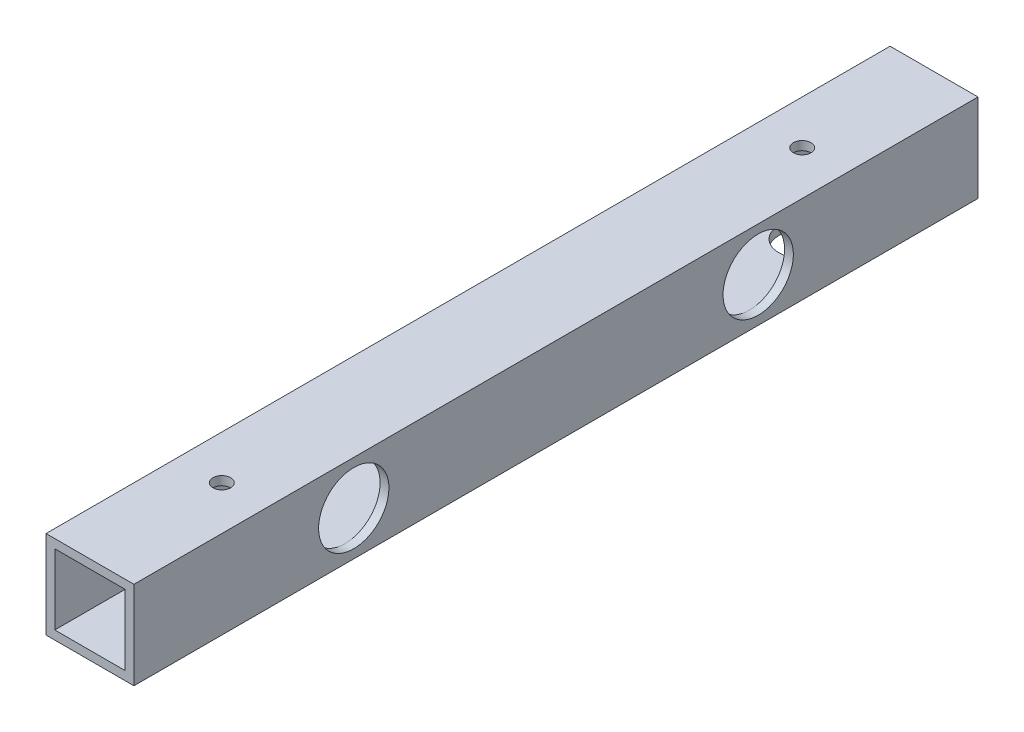
SolidWorks part; units mm, degrees
material "1060 合金"
ref_plane "正面" through (0, 0, 0) normal (0, 0, 1) x (1, 0, 0)
ref_plane "平面" through (0, 0, 0) normal (0, 1, 0) x (1, 0, 0)
ref_plane "右側面" through (0, 0, 0) normal (1, 0, 0) x (0, 0, -1)
sketch "ｽｹｯﾁ1" plane through (0, 0, 0) normal (0, 0, 1) x (1, 0, 0)
  line L1 (-7.0101, 7.7326) -> (7.9899, 7.7326)
  line L2 (-7.0101, 7.7326) -> (-7.0101, -7.2674)
  line L3 (-7.0101, -7.2674) -> (7.9899, -7.2674)
  line L4 (7.9899, 7.7326) -> (7.9899, -7.2674)
  line L9 (-5.5101, 6.2326) -> (6.4899, 6.2326)
  line L10 (-5.5101, 6.2326) -> (-5.5101, -5.7674)
  line L11 (-5.5101, -5.7674) -> (6.4899, -5.7674)
  line L12 (6.4899, 6.2326) -> (6.4899, -5.7674)
  dimension "D1" = 15
  dimension "D2" = 15
  dimension "D3" = 1.5
  dimension "D4" = 1.5
  dimension "D5" = 12
  dimension "D6" = 12
extrude "ﾎﾞｽ - 押し出し2" add sketch "ｽｹｯﾁ1" along normal blind 144
sketch "ｽｹｯﾁ2" plane through (-7.0101, 0, 0) normal (-1, 0, 0) x (0, 0, 1)
  line L0 (0, 0.2326) -> (72.5, 0.2326)
  line L1 (0, 7.7326) -> (0, -7.2674) construction
  circle A0 centre (72.5, 0.2326) radius 1.5
  dimension "D1" = 72.5
extrude "ｶｯﾄ - 押し出し1" cut sketch "ｽｹｯﾁ2" against normal blind 10
sketch "ｽｹｯﾁ3" plane through (0, 7.7326, 0) normal (0, 1, 0) x (1, 0, 0)
  line L0 (0.4899, 0) -> (0.4899, -22.5)
  line L1 (-7.0101, -144) -> (-7.0101, 0) construction
  circle A0 centre (0.4899, -22.5) radius 1.5
  dimension "D2" = 7.5
  dimension "D1" = 22.5
extrude "ｶｯﾄ - 押し出し2" cut sketch "ｽｹｯﾁ3" against normal blind 10
sketch "ｽｹｯﾁ4" plane through (0, 7.7326, 0) normal (0, 1, 0) x (1, 0, 0)
  line L0 (0.4899, -144) -> (0.4899, -121.5)
  line L2 (-7.0101, -144) -> (-7.0101, 0) construction
  circle A0 centre (0.4899, -121.5) radius 1.5
  dimension "D2" = 7.5
  dimension "D1" = 22.5
extrude "ｶｯﾄ - 押し出し4" cut sketch "ｽｹｯﾁ4" against normal blind 10
sketch "ｽｹｯﾁ6" plane through (-7.0101, 0, 0) normal (-1, 0, 0) x (0, 0, 1)
  line L0 (0, 0.2326) -> (7.5, 0.2326)
  line L1 (0, 7.7326) -> (0, -7.2674) construction
  circle A0 centre (7.5, 0.2326) radius 1.5
  dimension "D1" = 7.5
extrude "ｶｯﾄ - 押し出し5" cut sketch "ｽｹｯﾁ6" against normal blind 10
sketch "ｽｹｯﾁ7" plane through (0, -7.2674, 0) normal (0, -1, 0) x (1, 0, 0)
  line L0 (0.4899, 0) -> (0.4899, 22.5)
  line L1 (-7.0101, 0) -> (7.9899, 0) construction
  circle A0 centre (0.4899, 22.5) radius 4
  dimension "D1" = 22.5
extrude "ｶｯﾄ - 押し出し6" cut sketch "ｽｹｯﾁ7" against normal blind 10
sketch "ｽｹｯﾁ8" plane through (0, -7.2674, 0) normal (0, -1, 0) x (1, 0, 0)
  line L0 (0.4899, 144) -> (0.4899, 121.5)
  line L1 (-7.0101, 144) -> (7.9899, 144) construction
  circle A0 centre (0.4899, 121.5) radius 4
  dimension "D1" = 22.5
extrude "ｶｯﾄ - 押し出し7" cut sketch "ｽｹｯﾁ8" against normal blind 10
sketch "ｽｹｯﾁ9" plane through (-7.0101, 0, 0) normal (-1, 0, 0) x (0, 0, 1)
  line L0 (0, 0.2326) -> (37.5, 0.2326)
  line L1 (0, 7.7326) -> (0, -7.2674) construction
  circle A0 centre (37.5, 0.2326) radius 1.5
  dimension "D1" = 37.5
extrude "ｶｯﾄ - 押し出し8" cut sketch "ｽｹｯﾁ9" against normal blind 10
sketch "ｽｹｯﾁ10" plane through (7.9899, 0, 0) normal (1, 0, 0) x (0, 0, -1)
  line L0 (0, -7.2674) -> (0, 7.7326) construction
  line L1 (-144, 7.7326) -> (0, 7.7326) construction
  circle A0 centre (-37.5, 0.2326) radius 6
  dimension "D1" = 37.5
  dimension "D2" = 7.5
extrude "ｶｯﾄ - 押し出し9" cut sketch "ｽｹｯﾁ10" against normal blind 10
sketch "ｽｹｯﾁ11" plane through (0, -7.2674, 0) normal (0, -1, 0) x (1, 0, 0)
  line L0 (-7.0101, 144) -> (-7.0101, 0) construction
  line L1 (-7.0101, 0) -> (7.9899, 0) construction
  circle A0 centre (0.4899, 72.5) radius 4
  dimension "D1" = 7.5
  dimension "D2" = 72.5
extrude "ｶｯﾄ - 押し出し10" cut sketch "ｽｹｯﾁ11" against normal blind 10
sketch "ｽｹｯﾁ12" plane through (-7.0101, 0, 0) normal (-1, 0, 0) x (0, 0, 1)
  line L0 (144, 7.7326) -> (0, 7.7326) construction
  line L1 (144, 7.7326) -> (144, -7.2674) construction
  circle A0 centre (106.5, 0.2326) radius 1.5
  dimension "D1" = 7.5
  dimension "D2" = 37.5
extrude "ｶｯﾄ - 押し出し11" cut sketch "ｽｹｯﾁ12" against normal blind 10
sketch "ｽｹｯﾁ13" plane through (7.9899, 0, 0) normal (1, 0, 0) x (0, 0, -1)
  line L0 (-144, -7.2674) -> (-144, 7.7326) construction
  line L1 (-144, 7.7326) -> (0, 7.7326) construction
  circle A0 centre (-106.5, 0.2326) radius 6
  dimension "D1" = 37.5
  dimension "D2" = 7.5
extrude "ｶｯﾄ - 押し出し12" cut sketch "ｽｹｯﾁ13" against normal blind 10
